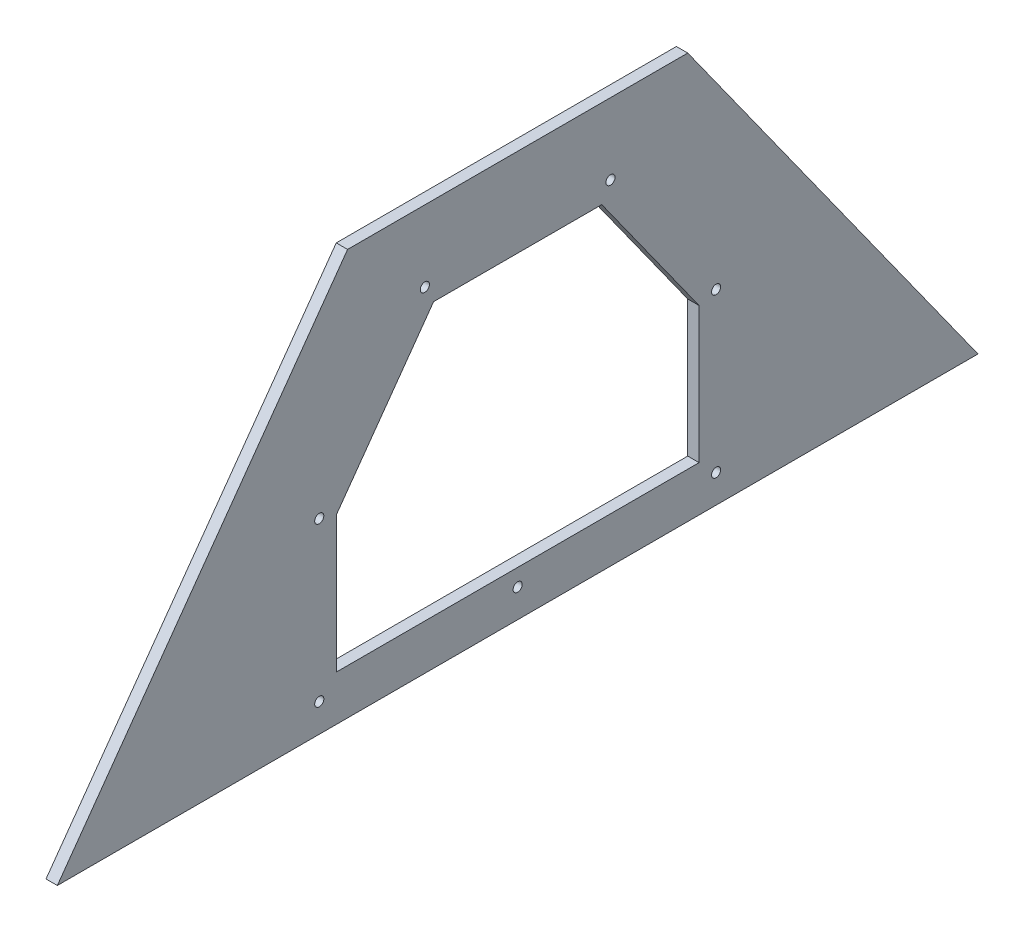
SolidWorks part; units mm, degrees
ref_plane "Front Plane" through (0, 0, 0) normal (0, 0, 1) x (1, 0, 0)
ref_plane "Top Plane" through (0, 0, 0) normal (0, 1, 0) x (1, 0, 0)
ref_plane "Right Plane" through (0, 0, 0) normal (1, 0, 0) x (0, 0, -1)
sketch "Sketch1" plane through (0, 0, 0) normal (1, 0, 0) x (0, 0, -1)
  line L0 (257.81, 0) -> (-257.81, 0)
  line L2 (-257.81, 0) -> (-95.25, 227.2413)
  line L3 (-95.25, 227.2413) -> (95.25, 227.2413)
  line L4 (257.81, 0) -> (95.25, 227.2413)
  point P4 (0, 227.2413)
  point P5 (0, 0)
  dimension "D1" = 279.4
  dimension "D2" = 515.62
  dimension "D3" = 190.5
extrude "Boss-Extrude1" add sketch "Sketch1" along normal blind 6.35
sketch "Sketch3" plane through (6.35, 0, 0) normal (1, 0, 0) x (0, 0, -1)
  line L0 (-95.25, 227.2413) -> (-257.81, 0) construction
  line L1 (-47.0893, 177.8) -> (47.0893, 177.8)
  line L2 (-101.6, 101.6) -> (-101.6, 25.4)
  line L3 (-101.6, 25.4) -> (101.6, 25.4)
  line L4 (101.6, 101.6) -> (101.6, 25.4)
  line L5 (-257.81, 0) -> (257.81, 0) construction
  line L6 (-101.6, 101.6) -> (-47.0893, 177.8)
  line L7 (47.0893, 177.8) -> (101.6, 101.6)
  point P0 (0, 25.4)
  dimension "D1" = 203.2
  dimension "D2" = 25.4
  dimension "D3" = 76.2
  dimension "D5" = 152.4
extrude "Cut-Extrude1" cut sketch "Sketch3" against normal through all
hole_wizard "#10 Clearance Hole1" positions "Sketch4" profile "Sketch5" hole size "#10" standard "ANSI Inch" end condition through all
sketch "Sketch4" plane through (6.35, 0, 0) normal (1, 0, 0) x (0, 0, -1)
  line L29 (51.9868, 187.325) -> (-51.9868, 187.325)
  line L30 (111.125, 104.6562) -> (51.9868, 187.325)
  line L31 (111.125, 15.875) -> (111.125, 104.6562)
  line L32 (-111.125, 15.875) -> (111.125, 15.875)
  line L33 (-111.125, 104.6562) -> (-111.125, 15.875)
  line L34 (-51.9868, 187.325) -> (-111.125, 104.6562)
  line L35 (51.9868, 187.325) -> (-51.9868, 187.325)
  line L36 (111.125, 104.6562) -> (51.9868, 187.325)
  line L37 (111.125, 15.875) -> (111.125, 104.6562)
  line L38 (-111.125, 15.875) -> (111.125, 15.875)
  line L39 (-111.125, 104.6562) -> (-111.125, 15.875)
  line L40 (-51.9868, 187.325) -> (-111.125, 104.6562)
  point P119 (51.9868, 187.325)
  point P120 (-51.9868, 187.325)
  point P121 (111.125, 104.6562)
  point P122 (111.125, 15.875)
  point P123 (-111.125, 15.875)
  point P124 (-111.125, 104.6562)
  point P137 (0, 15.875)
  dimension "D1" = 9.525
sketch "Sketch5" plane through (6.35, 187.325, -51.9868) normal (0, 1, 0) x (0, 0, -1)
  line L0 (0, 0) -> (0, 6.35)
  line L1 (0, 6.35) -> (2.5527, 6.35)
  line L2 (2.5527, 6.35) -> (2.5527, 0)
  line L5 (2.5527, 0) -> (0, 0)
  line L11 (0, -6.35) -> (0, 107.95) construction
  dimension "Thru Hole Dia." = 5.1054
  dimension "Thru Hole Depth" = 6.35
